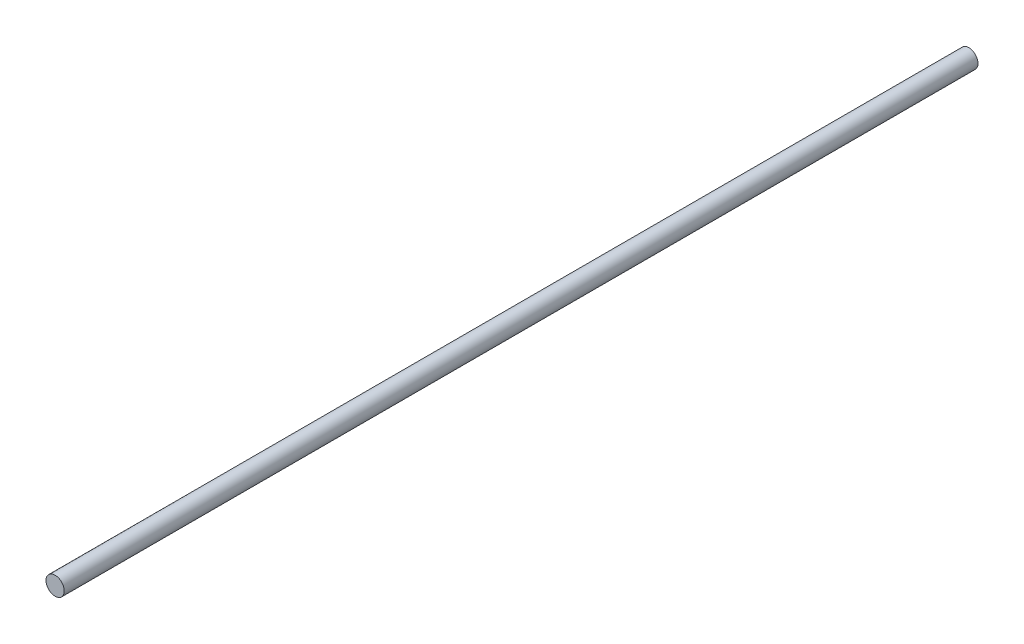
SolidWorks part; units mm, degrees
material "6063-T5"
ref_plane "Front Plane" through (0, 0, 0) normal (0, 0, 1) x (1, 0, 0)
ref_plane "Top Plane" through (0, 0, 0) normal (0, 1, 0) x (1, 0, 0)
ref_plane "Right Plane" through (0, 0, 0) normal (1, 0, 0) x (0, 0, -1)
sketch "Sketch1" plane through (0, 0, 0) normal (0, 0, 1) x (1, 0, 0)
  circle A0 centre (0, 0) radius 1.5
  dimension "D1" = 3
extrude "Boss-Extrude1" add sketch "Sketch1" along normal blind 150
